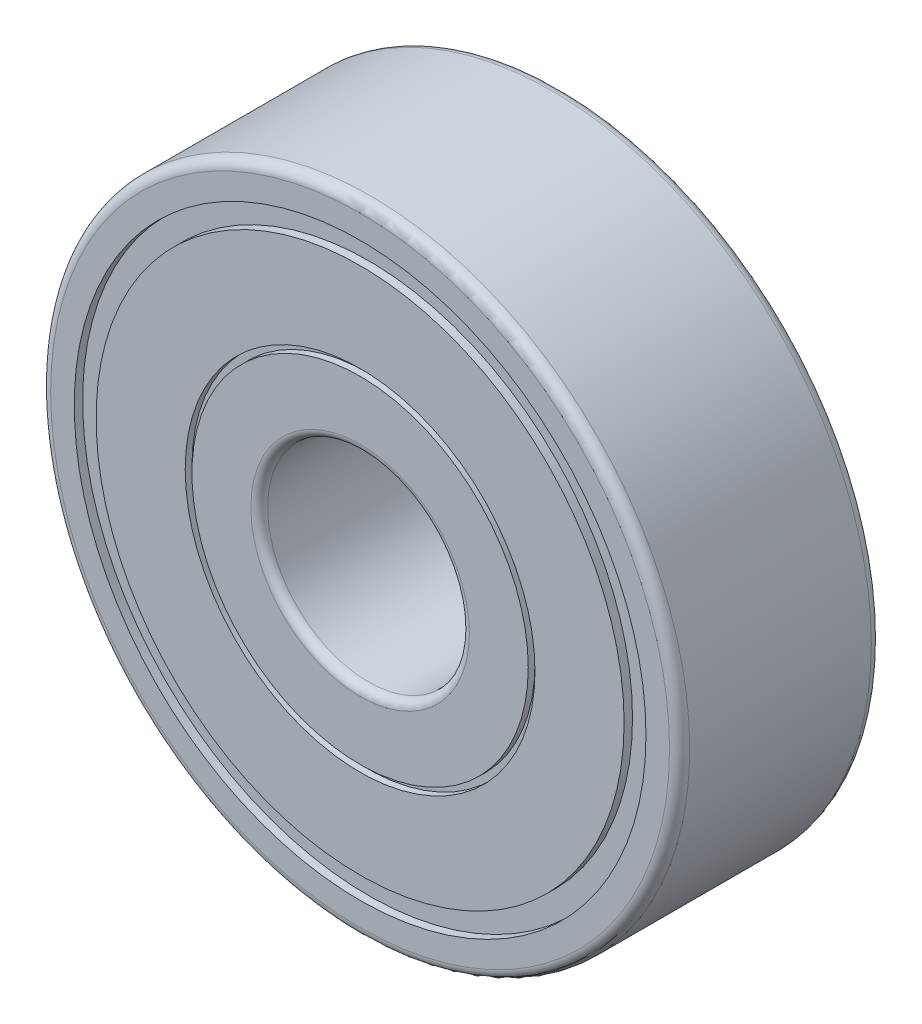
SolidWorks part; units mm, degrees
material "1023 Carbon Steel Sheet (SS)"
ref_plane "Front Plane" through (0, 0, 0) normal (0, 0, 1) x (1, 0, 0)
ref_plane "Top Plane" through (0, 0, 0) normal (0, 1, 0) x (1, 0, 0)
ref_plane "Right Plane" through (0, 0, 0) normal (1, 0, 0) x (0, 0, -1)
sketch "Sketch1" plane through (0, 0, 0) normal (0, 0, 1) x (1, 0, 0)
  circle A0 centre (0, 0) radius 9.5
  circle A1 centre (0, 0) radius 3
  dimension "D1" = 19
  dimension "D2" = 6
extrude "Boss-Extrude1" add sketch "Sketch1" along normal blind 6
sketch "Sketch2" plane through (0, 0, 6) normal (0, 0, 1) x (1, 0, 0)
  circle A0 centre (0, 0) radius 5.2
  circle A1 centre (0, 0) radius 5
  dimension "D1" = 10
  dimension "D2" = 10.4
extrude "Cut-Extrude1" cut sketch "Sketch2" against normal blind 0.2
sketch "Sketch3" plane through (0, 0, 6) normal (0, 0, 1) x (1, 0, 0)
  circle A0 centre (0, 0) radius 8.5
  circle A1 centre (0, 0) radius 7.85
  dimension "D1" = 17
  dimension "D2" = 15.7
extrude "Cut-Extrude2" cut sketch "Sketch3" against normal blind 0.25
ref_plane "Plane1" through (0, 0, 3) normal (0, 0, 1) x (1, 0, 0)
mirror "Mirror1" about plane through (0, 0, 3) normal (0, 0, 1) of "Cut-Extrude1", "Cut-Extrude2"
fillet "Fillet1" radius 0.3 2 edges at (9.5, 0, 0) (9.5, 0, 6)
fillet "Fillet2" radius 0.25 2 edges at (3, 0, 0) (3, 0, 6)
